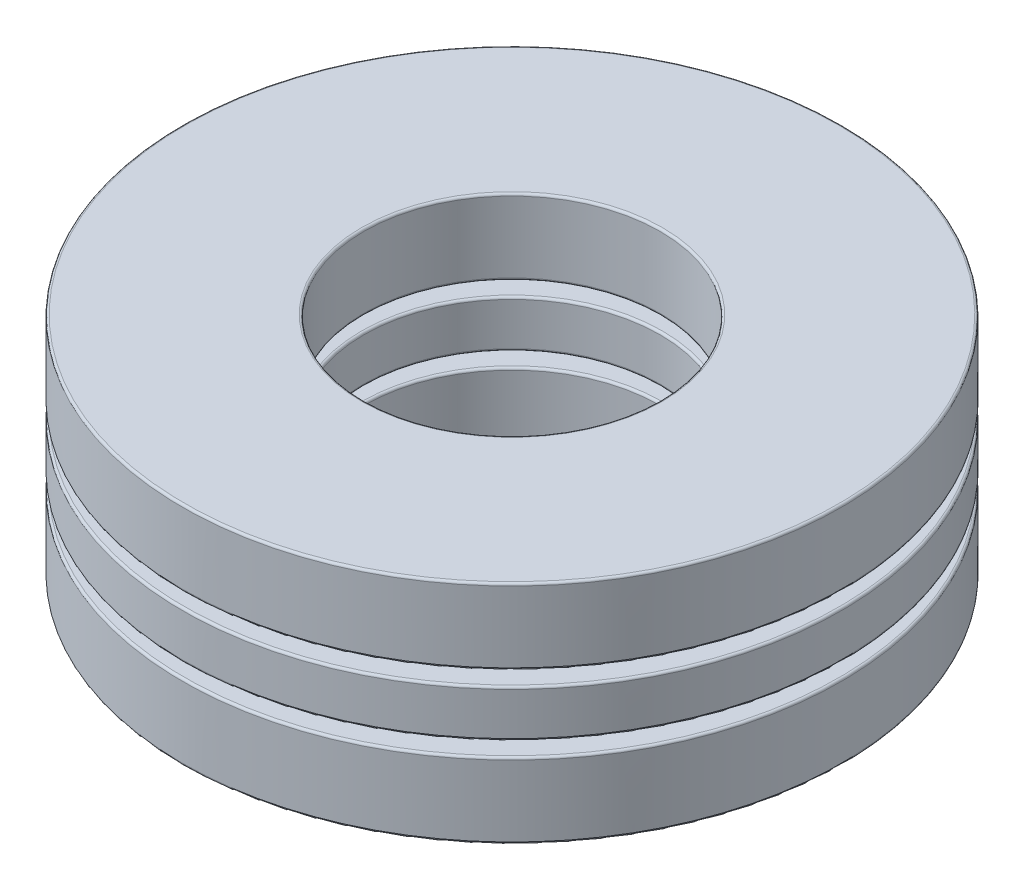
SolidWorks part; units mm, degrees
ref_plane "Front Plane" through (0, 0, 0) normal (0, 0, 1) x (1, 0, 0)
ref_plane "Top Plane" through (0, 0, 0) normal (0, 1, 0) x (1, 0, 0)
ref_plane "Right Plane" through (0, 0, 0) normal (1, 0, 0) x (0, 0, -1)
sketch "Sketch1" plane through (0, 0, 0) normal (1, 0, 0) x (0, 0, -1)
  line L0 (-7.1437, 0) -> (7.1437, 0) construction
  line L1 (0, -2.4511) -> (0, 2.4511) construction
  line L2 (-7.1437, 0.5106) -> (-3.2131, 0.5106)
  line L3 (-7.1437, 0.5106) -> (-7.1437, -0.5106)
  line L4 (-7.1437, -0.5106) -> (-3.2131, -0.5106)
  line L5 (-3.2131, 0.5106) -> (-3.2131, -0.5106)
  line L6 (-5.1784, 0.817) -> (-5.1784, -0.817) construction
  circle A0 centre (-5.1784, 0) radius 0.817 construction
  point P13 (-5.1784, 0.5106)
  dimension "OD" = 14.2875
  dimension "Shaft Dia" = 6.4262
  dimension "Th" = 4.9022
  dimension "D1" = 1.6341
  dimension "D2" = 1.0213
revolve "Revolve1" add sketch "Sketch1" angle 360 about L1
sketch "Sketch3" plane through (0, 0, 0) normal (1, 0, 0) x (0, 0, -1)
  line L0 (-5.1784, 0.817) -> (-5.1784, -0.817)
  arc A0 (-5.1784, 0.817) -> (-5.1784, -0.817) centre (-5.1784, 0) ccw
  circle A1 centre (-5.1784, 0) radius 0.817 construction
revolve "Cut-Revolve1" cut sketch "Sketch3" angle 360 about L0
sketch "Sketch2" plane through (0, 0, 0) normal (1, 0, 0) x (0, 0, -1)
  line L0 (-5.1784, 0.817) -> (-5.1784, -0.817)
  arc A0 (-5.1784, 0.817) -> (-5.1784, -0.817) centre (-5.1784, 0) ccw
  circle A2 centre (-5.1784, 0) radius 0.817 construction
revolve "Revolve2" add sketch "Sketch2" angle 360 about L0
ref_axis "Axis1" through (0, 2.4511, 0) along (0, -1, 0)
pattern_circular "CirPattern1" count 3 every 120 about axis through (0, 2.4511, 0) along (0, -1, 0) of bodies 187
pattern_circular "CirPattern2" count 3 every 120 about axis through (0, 0, 0) along (0, 1, 0) of "Cut-Revolve1"
sketch "Sketch4" plane through (0, 0, 0) normal (1, 0, 0) x (0, 0, -1)
  line L0 (-7.1437, 0.5106) -> (-7.1437, -0.5106) construction
  line L1 (-7.1437, 0.817) -> (-3.2131, 0.817)
  line L2 (-7.1437, 0.817) -> (-7.1437, 2.4511)
  line L3 (-7.1437, 2.4511) -> (-3.2131, 2.4511)
  line L4 (-3.2131, 0.817) -> (-3.2131, 2.4511)
  line L5 (-7.1437, -2.4511) -> (-3.2131, -2.4511)
  line L6 (-7.1437, -2.4511) -> (-7.1437, -0.817)
  line L7 (-7.1437, -0.817) -> (-3.2131, -0.817)
  line L8 (-3.2131, -2.4511) -> (-3.2131, -0.817)
  line L9 (-5.1784, 0.817) -> (-5.1784, -0.817) construction
  line L10 (-3.2131, 0.5106) -> (-3.2131, -0.5106) construction
  line L11 (0, 0) -> (-7.1437, 0) construction
  line L12 (-7.1437, 0) -> (7.1437, 0) construction
  dimension "Ht" = 4.9022
revolve "Revolve3" add sketch "Sketch4" angle 360 about L1
fillet "Fillet1" radius 0.049 4 edges at (0, 0.817, -3.2131) (0, 2.4511, -3.2131) (0, 0.817, -7.1437) (0, 2.4511, -7.1437)
fillet "Fillet2" radius 0.049 4 edges at (0, -0.5106, -3.2131) (0, 0.5106, -3.2131) (0, -0.5106, -7.1437) (0, 0.5106, -7.1437)
fillet "Fillet3" radius 0.049 4 edges at (0, -2.4511, -3.2131) (0, -0.817, -3.2131) (0, -2.4511, -7.1437) (0, -0.817, -7.1437)
equation "\"D1@Sketch1\" = \"Th@Sketch1\"/3"
equation "\"D2@Sketch1\" = \"D1@Sketch1\"*.625"
equation "\"Balls@CirPattern1\" = \"OD@Sketch1\"*5"
equation "\"Angle@CirPattern1\" = 360/\"Balls@CirPattern1\""
equation "\"D1@CirPattern2\" = \"Balls@CirPattern1\""
equation "\"D2@CirPattern2\" = \"Angle@CirPattern1\""
equation "\"D1@Fillet1\" = \"Th@Sketch1\"*.01"
equation "\"D1@Fillet2\" = \"D1@Fillet1\""
equation "\"D1@Fillet3\" = \"D1@Fillet1\""
